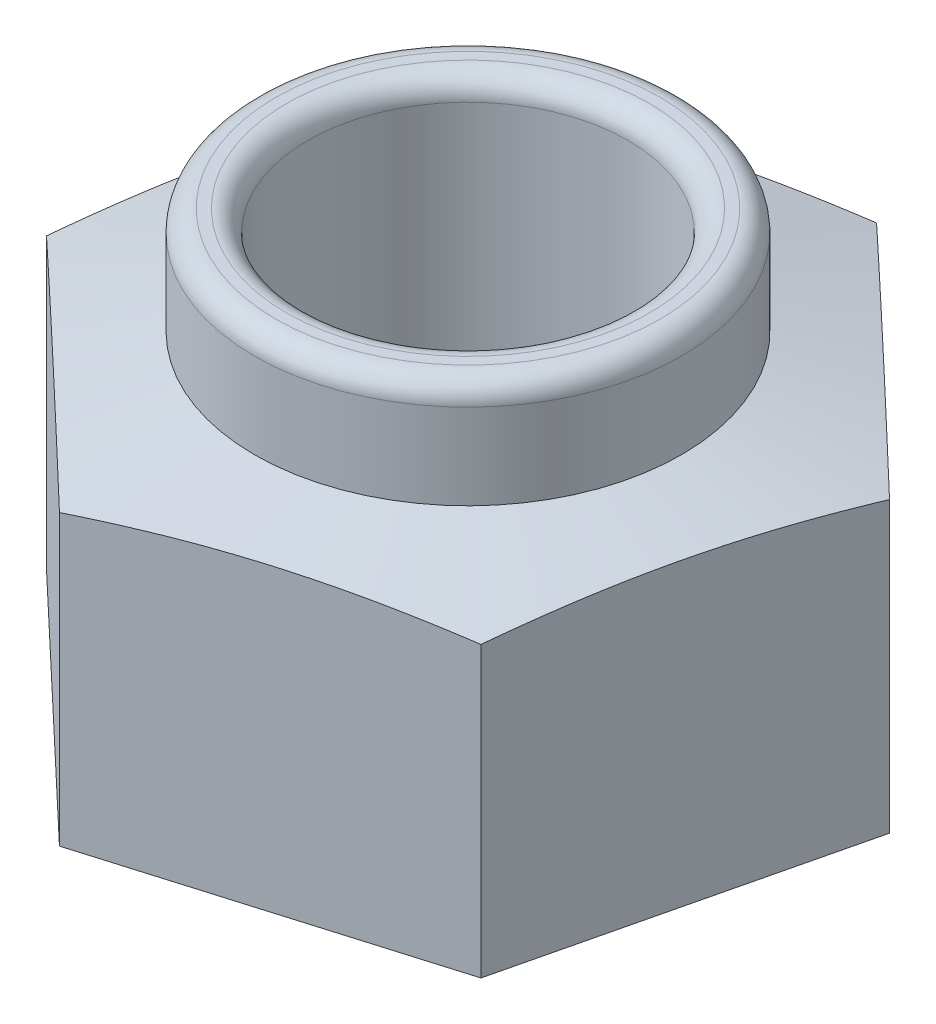
SolidWorks part; units mm, degrees
ref_plane "前视基准面" through (0, 0, 0) normal (0, 0, 1) x (1, 0, 0)
ref_plane "上视基准面" through (0, 0, 0) normal (0, 1, 0) x (1, 0, 0)
ref_plane "右视基准面" through (0, 0, 0) normal (1, 0, 0) x (0, 0, -1)
sketch "草图1" plane through (0, 0, 0) normal (0, 1, 0) x (1, 0, 0)
  line L1 (2.3052, -2.1839) -> (3.0439, 0.9044)
  line L2 (3.0439, 0.9044) -> (0.7387, 3.0883)
  line L3 (0.7387, 3.0883) -> (-2.3052, 2.1839)
  line L4 (-2.3052, 2.1839) -> (-3.0439, -0.9044)
  line L5 (-3.0439, -0.9044) -> (-0.7387, -3.0883)
  line L6 (-0.7387, -3.0883) -> (2.3052, -2.1839)
  circle A0 centre (0, 0) radius 1.5
  circle A1 centre (0, 0) radius 2.75 construction
  dimension "D1" = 3
  dimension "D2" = 5.5
extrude "凸台-拉伸1" add sketch "草图1" along normal blind 4
sketch "草图2" plane through (0, 0, 0) normal (0, 0, 1) x (1, 0, 0)
  line L0 (-4, 2.5) -> (-2, 3)
  line L2 (-2, 3) -> (-2, 4)
  line L3 (-3.0439, 4) -> (-0.7387, 4) construction
  line L4 (-2, 4) -> (-4, 4)
  line L5 (-4, 4) -> (-4, 2.5)
  line L6 (0, 4) -> (0, 0) construction
  point P2 (-3.2465, 2.771)
  dimension "D1" = 2
  dimension "D2" = 2
  dimension "D3" = 1
  dimension "D4" = 1.5
revolve "切除-旋转1" cut sketch "草图2" angle 360 about axis through (0, 4, 0) along (0, -1, 0)
fillet "圆角2" radius 0.2 2 edges at (0, 4, 1.5) (0, 4, 2)
